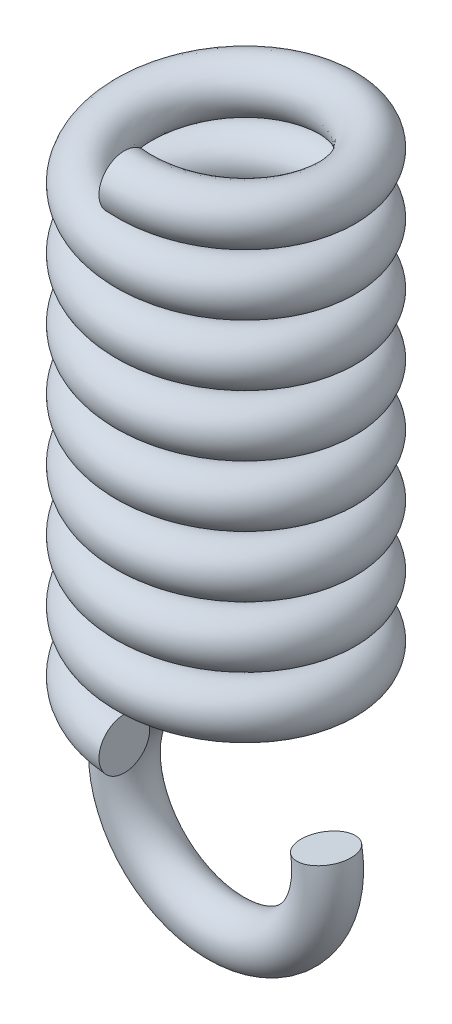
SolidWorks part; units mm, degrees
ref_plane "前视基准面" through (0, 0, 0) normal (0, 0, 1) x (1, 0, 0)
ref_plane "上视基准面" through (0, 0, 0) normal (0, 1, 0) x (1, 0, 0)
ref_plane "右视基准面" through (0, 0, 0) normal (1, 0, 0) x (0, 0, -1)
sketch "草图1" plane through (0, 0, 0) normal (0, 0, 1) x (1, 0, 0)
  line L0 (0, 0) -> (0, 45.627)
  circle A0 centre (10, 0) radius 2.5
sketch "草图2" plane through (0, 0, 0) normal (0, 1, 0) x (1, 0, 0)
  circle A0 centre (0, 0) radius 10
curve "螺旋线/涡状线1" pitch 6 height 48 turns 8
sweep "扫描1" add profiles "草图1" path "螺旋线/涡状线1"
sketch "草图5" plane through (0, 0, 0) normal (1, 0, 0) x (0, 0, -1)
  circle A1 centre (0, -5.2433) radius 2.5
sketch "草图6" plane through (0, 0, 0) normal (0, 0, 1) x (1, 0, 0)
  line L0 (0, -7.7433) -> (0, -2.7433) construction
  arc A0 (0, -5.2433) -> (9.8481, -13.5069) centre (0, -15.2433) ccw
  point P5 (0, 0)
sweep "扫描2" add profiles "草图5" path "草图6"
sketch "草图9" plane through (0, 0, 0) normal (1, 0, 0) x (0, 0, -1)
  circle A0 centre (-10, -4.5) radius 2.5
sketch "草图11" plane through (2.6068, -14.7837, 0) normal (-0.1736, 0.9848, 0) x (0.9848, 0.1736, 0)
  circle A0 centre (7.353, 0) radius 2.5
